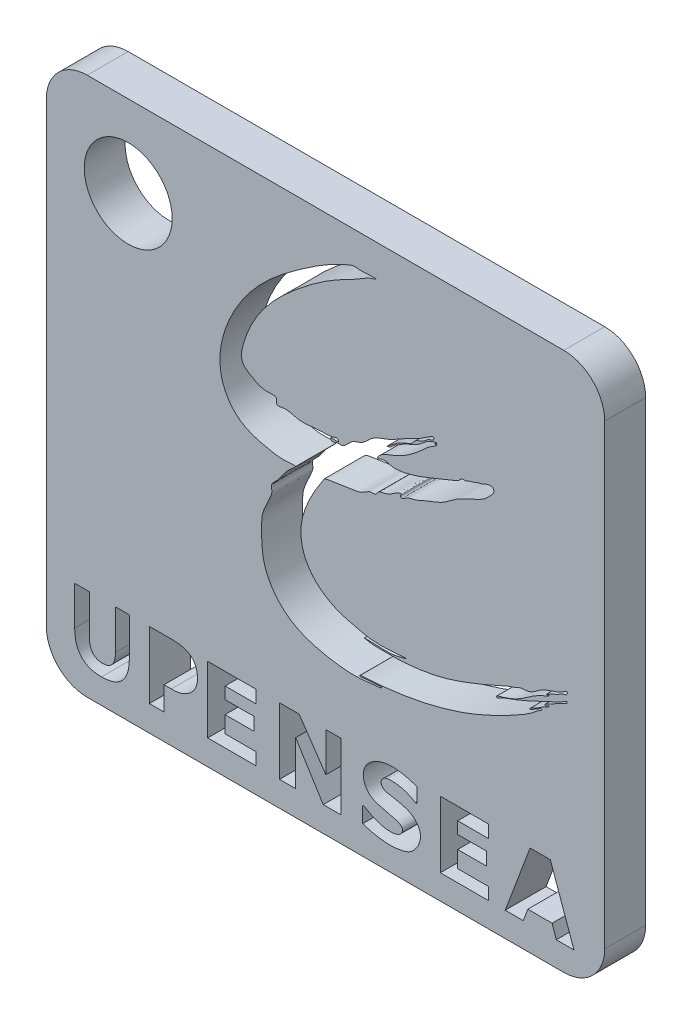
SolidWorks part; units mm, degrees
ref_plane "Plan de face" through (0, 0, 0) normal (0, 0, 1) x (1, 0, 0)
ref_plane "Plan de dessus" through (0, 0, 0) normal (0, 1, 0) x (1, 0, 0)
ref_plane "Plan de droite" through (0, 0, 0) normal (1, 0, 0) x (0, 0, -1)
sketch "Esquisse1" plane through (0, 0, 0) normal (0, 0, 1) x (1, 0, 0)
  line L0 (-81.1421, -32.8342) -> (-69.3736, -32.8342)
  line L1 (-69.3736, -32.8342) -> (-69.3736, -35.921)
  line L2 (-69.3736, -35.921) -> (-76.8977, -35.921)
  line L3 (-76.8977, -35.921) -> (-76.8977, -38.8149)
  line L4 (-76.8977, -38.8149) -> (-69.8674, -38.8149)
  line L5 (-69.8674, -38.8149) -> (-69.8674, -41.9917)
  line L6 (-69.8674, -41.9917) -> (-76.8977, -41.9917)
  line L7 (-76.8977, -41.9917) -> (-76.8977, -46.0504)
  line L8 (-76.8977, -46.0504) -> (-69.3736, -46.0504)
  line L9 (-69.3736, -46.0504) -> (-69.3736, -49.04)
  line L10 (-69.3736, -49.04) -> (-81.1421, -49.04)
  line L11 (-81.1421, -49.04) -> (-81.1421, -32.8342)
  line L12 (-63.6027, -32.8342) -> (-58.792, -32.8342)
  line L13 (-58.792, -32.8342) -> (-52.2677, -42.3901)
  line L14 (-52.2677, -42.3901) -> (-52.2677, -32.8342)
  line L15 (-52.2677, -32.8342) -> (-48.5742, -32.8342)
  line L16 (-48.5742, -32.8342) -> (-48.5742, -49.04)
  line L17 (-48.5742, -49.04) -> (-52.9133, -49.04)
  line L18 (-52.9133, -49.04) -> (-59.644, -38.2361)
  line L19 (-59.644, -38.2361) -> (-59.644, -49.04)
  line L20 (-59.644, -49.04) -> (-63.6027, -49.04)
  line L21 (-63.6027, -49.04) -> (-63.6027, -32.8342)
  line L22 (-24.3175, -32.95) -> (-12.549, -32.95)
  line L23 (-12.549, -32.95) -> (-12.549, -36.0368)
  line L24 (-12.549, -36.0368) -> (-20.0731, -36.0368)
  line L25 (-20.0731, -36.0368) -> (-20.0731, -38.9307)
  line L26 (-20.0731, -38.9307) -> (-13.0428, -38.9307)
  line L27 (-13.0428, -38.9307) -> (-13.0428, -42.1075)
  line L28 (-13.0428, -42.1075) -> (-20.0731, -42.1075)
  line L29 (-20.0731, -42.1075) -> (-20.0731, -46.1662)
  line L30 (-20.0731, -46.1662) -> (-12.549, -46.1662)
  line L31 (-12.549, -46.1662) -> (-12.549, -49.1558)
  line L32 (-12.549, -49.1558) -> (-24.3175, -49.1558)
  line L33 (-24.3175, -49.1558) -> (-24.3175, -32.95)
  line L34 (-2.3808, -32.95) -> (-8.462, -49.1558)
  line L35 (-4.0553, -49.1558) -> (-2.9335, -46.1662)
  line L36 (-2.9335, -46.1662) -> (3.0043, -46.1662)
  line L37 (3.0043, -46.1662) -> (4.0312, -49.1558)
  line L38 (4.0312, -49.1558) -> (8.3413, -49.1558)
  line L39 (8.3413, -49.1558) -> (2.5681, -32.95)
  line L40 (2.5681, -32.95) -> (-2.3808, -32.95)
  line L41 (0.0936, -37.3658) -> (1.9922, -42.8931)
  line L42 (1.9922, -42.8931) -> (-1.9654, -42.8931)
  line L43 (-1.9654, -42.8931) -> (0.0936, -37.3658)
  line L44 (-4.0553, -49.1558) -> (-8.462, -49.1558)
  line L45 (-30.0084, -33.7556) -> (-30.0084, -37.3658)
  line L46 (-30.0084, -37.3658) -> (-30.4403, -37.3658)
  line L47 (-43.2668, -44.5326) -> (-43.2668, -48.2453)
  line L49 (-120.5635, 76.467) -> (15.8561, 76.467)
  line L50 (-120.5635, 76.467) -> (-120.5635, -55.1571)
  line L51 (-120.5635, -55.1571) -> (15.8561, -55.1571)
  line L52 (15.8561, 76.467) -> (15.8561, -55.1571)
  circle A0 centre (-100.5635, 56.467) radius 10.7431
  spline S0 degree 3 poles (-52.6521, 20.0262) (-55.3334, 15.9515) (-60.2486, 7.9887) (-56.1162, -2.7779) (-49.9463, -6.2531) (-43.7235, -7.7216) (-40.6217, -8.8443) (-31.2107, -7.7102) (-35.4931, -8.7951) (-37.2317, -9.0197) (-44.5779, -8.4799) (-40.3233, -9.2515) (-38.1518, -9.1057) (-34.4042, -9.2177) (-29.4978, -8.7751) (-20.8331, -7.3091) (-9.8092, -2.3246) (-7.1565, -1.1405) (-5.6286, -0.6952) (-4.9048, -0.2341) (-3.9906, -0.1272) (-1.9518, -0.1849) (-0.2604, 1.9411) (3.4935, 3.0196) (5.3244, 3.8516) (6.7532, 4.8305) (6.7243, 3.7436) (5.7681, 3.7921) (4.2536, 2.7443) (3.1571, 2.4856) (1.5619, 1.5963) (1.9771, 1.4735) (2.3772, 1.8572) (2.2067, 1.5592) (2.1336, 1.4391) (2.1304, 1.4338) knots 0 0 0 0 0.034118 0.050236 0.068967 0.0735 0.095563 0.104191 0.107922 0.116908 0.126964 0.13031 0.137621 0.14482 0.154993 0.171422 0.207781 0.216896 0.21919 0.229442 0.232265 0.24613 0.386673 0.489154 0.601852 0.608768 0.628384 0.656974 0.686943 0.800375 0.806976 0.814482 0.827885 0.837106 0.837535 0.837535 0.837535 0.837535
  spline S1 degree 3 poles (2.1304, 1.4338) (-3.2143, -0.4983) (-3.5636, -3.1574) (-10.7433, -4.8196) (-10.4207, -5.2619) (-10.0076, -5.0191) (-9.1355, -4.4797) (-6.2924, -3.5462) (-2.2057, -1.8343) (2.6217, 0.5739) (5.1274, 1.6237) (6.7268, 2.6931) (6.7061, 2.0367) (6.1892, 2.0349) (5.6903, 1.5221) (4.621, 1.2435) (3.4802, 0.3835) (2.2151, -0.1297) (1.5935, -0.5477) (1.0869, -0.7912) (1.5087, -1.1167) (1.7441, -0.7689) (2.0279, -0.5527) (2.3778, -0.8038) (1.8965, -0.8769) (1.6097, -1.1864) (0.7544, -1.491) (-0.2683, -2.2868) (-1.4781, -2.9352) (-2.2533, -3.2224) (-2.5669, -3.6281) (-1.7593, -3.506) (-1.4045, -2.961) (-0.3761, -2.6651) (0.0243, -2.1587) (0.5176, -2.1417) (0.3842, -2.5623) (-0.1273, -2.6442) (-0.7211, -3.1586) (-2.3341, -4.566) (-7.4709, -7.5112) (-19.2478, -13.4595) (-32.514, -16.378) (-41.7877, -17.0094) (-43.6311, -17.0895) (-43.832, -17.1275) (-44.0811, -17.3149) (-43.5984, -17.4832) (-43.0648, -17.2603) (-42.2857, -17.3044) (-41.9929, -17.2707) knots 0 0 0 0 0.134848 0.143034 0.144602 0.148639 0.15418 0.178068 0.234678 0.292201 0.330746 0.333193 0.337239 0.34163 0.346585 0.358072 0.373748 0.389768 0.396913 0.399366 0.402749 0.405986 0.410304 0.412056 0.415103 0.419095 0.426513 0.440579 0.458948 0.465949 0.467501 0.470952 0.480464 0.491217 0.499184 0.500837 0.502285 0.509316 0.515196 0.525664 0.573905 0.691977 0.923329 0.972552 0.974531 0.977935 0.97947 0.981332 0.988582 1 1 1 1
  spline S2 degree 3 poles (-41.9929, -17.2707) (-41.9788, -17.2837) (-39.8428, -17.181) (-38.755, -16.9729) (-38.5663, -17.0696) (-38.6975, -17.3571) (-38.8106, -17.3428) (-38.9909, -17.3428) knots 0 0 0 0 0.789101 0.825842 0.866785 0.917494 1 1 1 1
  spline S3 degree 3 poles (-38.9909, -17.3428) (-41.4072, -17.6298) (-45.2552, -18.1586) (-52.8341, -17.1941) (-61.3994, -15.1557) (-68.0331, -6.4333) (-67.9639, 0.274) (-67.9478, 5.786) (-66.0715, 8.6338) (-65.3184, 11.1565) (-65.8748, 12.393) (-64.1051, 13.8198) (-62.6773, 15.9813) (-61.4735, 17.5888) (-59.1059, 19.3906) (-63.2666, 18.8642) (-66.4685, 19.585) (-72.9268, 21.0498) (-80.9751, 30.5359) (-74.113, 49.4377) (-60.0056, 60.7329) (-50.3924, 66.8729) (-45.5535, 68.7199) (-44.2361, 68.5409) (-42.7435, 68.5663) (-38.9093, 68.8413) (-41.9561, 67.9964) (-44.3031, 66.3257) (-50.0489, 63.6386) (-58.0968, 58.1526) (-67.1463, 50.1111) (-71.8026, 41.7282) (-73.4928, 34.6163) (-69.7732, 32.4272) (-67.6012, 31.1924) (-64.2264, 31.7212) (-64.3925, 30.572) (-64.2794, 29.6066) (-61.7144, 30.4334) (-58.8055, 28.8928) (-54.2716, 29.9061) (-51.3045, 29.5246) (-49.4313, 30.3609) (-48.9, 29.4447) (-50.1299, 29.5407) (-51.4905, 29.5283) (-50.5578, 28.6216) (-49.637, 29.3856) (-47.6915, 28.9538) (-46.3674, 31.58) (-43.2546, 31.9776) (-40.8927, 35.0774) (-36.4966, 36.0563) (-31.9864, 39.1871) (-29.4686, 39.8946) (-25.6893, 42.7432) (-25.9981, 41.2912) (-27.0909, 41.3145) (-27.9761, 40.3733) (-29.141, 39.7498) (-30.483, 39.3097) (-31.3078, 37.9953) (-33.1588, 37.4839) (-35.0845, 36.3905) (-36.0606, 35.4678) (-37.8011, 34.347) (-36.1873, 34.9009) (-35.6812, 35.6441) (-34.2101, 36.4274) (-32.8831, 37.4122) (-30.9675, 38.0047) (-28.5056, 39.4567) (-27.3907, 41.0171) (-25.0035, 41.395) (-25.3264, 41.0299) (-25.3331, 41.1161) (-25.6368, 40.9763) knots 0 0 0 0 0.026687 0.041759 0.083493 0.118973 0.15054 0.156598 0.176995 0.180173 0.185825 0.19148 0.201603 0.213818 0.218107 0.223796 0.242243 0.2661 0.288782 0.36971 0.440445 0.490023 0.491708 0.496504 0.503315 0.512758 0.517467 0.527117 0.549028 0.582505 0.635087 0.675369 0.692164 0.702026 0.71711 0.724427 0.726292 0.728748 0.733278 0.748051 0.765921 0.779575 0.782783 0.784337 0.788152 0.791967 0.793474 0.798863 0.80206 0.813838 0.823241 0.834393 0.853281 0.871386 0.888313 0.896676 0.897774 0.902185 0.905809 0.911659 0.916426 0.920643 0.927543 0.936656 0.942844 0.946607 0.949758 0.954208 0.957935 0.967061 0.972246 0.979627 0.996876 0.997506 0.998263 1 1 1 1
  spline S4 degree 3 poles (-25.6368, 40.9763) (-25.6733, 40.8054) (-25.4242, 40.938) (-25.0658, 40.9051) (-25.4396, 40.5844) (-25.8747, 40.3011) (-26.9416, 39.7153) (-28.3291, 38.4028) (-31.0963, 35.9972) (-34.7385, 33.4962) (-38.854, 32.4513) (-39.6122, 31.096) (-39.7178, 30.921) (-39.2618, 30.8129) (-38.928, 31.1404) (-38.1449, 31.2357) (-37.2797, 31.2884) (-36.2001, 30.8875) (-34.9991, 30.7965) (-32.3007, 31.1843) (-28.8775, 32.2666) (-24.6192, 34.0657) (-21.6074, 35.2324) (-19.6403, 36.1048) (-19.1108, 36.9743) (-18.1402, 36.731) (-17.3166, 37.2696) (-16.1544, 37.4755) (-15.2088, 37.9964) (-14.0495, 38.132) (-13.2111, 38.6955) (-12.3008, 38.8984) (-11.3558, 38.8479) (-11.0854, 37.8223) (-11.9956, 36.8135) (-13.395, 35.2514) (-16.5811, 33.7226) (-20.3331, 32.1581) (-23.7739, 29.1421) (-27.355, 28.1263) (-30.3376, 26.5095) (-32.2613, 26.4358) (-33.7875, 25.052) (-34.1352, 25.8254) (-33.5394, 26.4287) (-34.8709, 25.9786) (-35.5281, 25.5291) (-36.741, 24.6683) (-38.1132, 24.2688) (-39.5275, 24.0111) (-40.0047, 22.7863) (-41.1338, 23.0436) (-42.3071, 22.5053) (-43.7847, 21.3791) (-46.3622, 21.215) (-49.3402, 20.5183) (-51.5236, 20.4601) (-52.6521, 20.0262) knots 0 0 0 0 0.003835 0.005626 0.00865 0.013337 0.025485 0.043794 0.074034 0.138519 0.186487 0.188036 0.18927 0.191769 0.197818 0.204074 0.215307 0.224789 0.239449 0.252379 0.309643 0.350812 0.396295 0.411559 0.416285 0.42557 0.437284 0.446181 0.46202 0.470349 0.48205 0.492444 0.500051 0.507958 0.519114 0.539936 0.574207 0.626742 0.667092 0.713693 0.742758 0.767935 0.781266 0.784831 0.790075 0.797681 0.809789 0.823175 0.84057 0.856115 0.863527 0.876386 0.884884 0.903947 0.932867 0.962689 1 1 1 1
  spline S5 degree 3 poles (-66.3705, -0.6372) (-66.2426, -3.307) (-66.2081, -4.4798) (-65.0585, -6.4613) (-63.8673, -8.1484) (-63.6964, -8.3653) (-63.7281, -8.1137) (-63.7348, -8.1525) (-63.8418, -7.9649) (-63.8834, -7.8805) (-63.9419, -7.6812) knots 0 0 0 0 0.53075 0.866804 0.910185 0.922558 0.935229 0.965645 0.972122 1 1 1 1
  spline S6 degree 3 poles (-63.9419, -7.6812) (-64.7159, -5.3195) (-65.7948, -3.066) (-66.3705, -0.6372) knots 0 0 0 0 1 1 1 1
  spline S7 degree 3 poles (-62.5352, -10.5523) (-63.6787, -9.4519) (-63.2343, -10.5737) (-62.6831, -11.0949) (-61.8406, -11.8438) (-61.4717, -12.1252) (-61.047, -12.4765) (-61.089, -12.1979) (-61.2166, -12.0257) (-61.5343, -11.6826) (-62.0825, -11.0825) (-62.5352, -10.5523) (-63.6787, -9.4519) (-63.2343, -10.5737) knots -0.402191 -0.295019 -0.119537 0 0.066805 0.227094 0.37929 0.471781 0.501895 0.514205 0.563001 0.597809 0.704981 0.880463 1 1.066805 1.227094 1.37929 only from (-63.5047, -9.7729) to (-63.5047, -9.7729)
  spline S8 degree 3 poles (-30.0084, -33.7556) (-32.645, -32.8965) (-37.1136, -31.7547) (-42.1383, -34.3995) (-43.5351, -37.9134) (-42.2928, -41.3103) (-39.0211, -42.4726) (-36.4644, -43.0591) (-34.5429, -43.4994) (-33.4189, -44.3949) (-33.6635, -45.5813) (-34.9075, -46.4708) (-37.0204, -46.6611) (-39.6413, -46.0975) (-41.6577, -45.1439) (-42.7569, -44.4019) (-43.2336, -44.3001) (-43.2668, -44.5326) knots 0 0 0 0 0.213305 0.332543 0.387996 0.489669 0.562609 0.640595 0.690513 0.712561 0.740192 0.766735 0.824594 0.893931 0.970764 0.987194 1 1 1 1
  spline S9 degree 3 poles (-30.4403, -37.3658) (-32.1696, -36.2135) (-34.6764, -35.5022) (-37.9246, -35.6751) (-39.0034, -37.0045) (-38.3722, -38.5423) (-36.2028, -38.9167) (-33.6935, -39.3132) (-30.7247, -40.385) (-28.6088, -43.3373) (-29.6785, -46.5114) (-31.5752, -48.5521) (-36.1582, -49.9657) (-40.259, -49.2481) (-43.2668, -48.2453) knots 0 0 0 0 0.15292 0.204126 0.234845 0.267869 0.309745 0.39187 0.468931 0.544719 0.643629 0.695197 0.754799 1 1 1 1
  point P97 (-66.2687, -2.6021)
  point P315 (0, 0)
  dimension "D1" = 20
  dimension "D2" = 20
extrude "Boss.-Extru.1" add sketch "Esquisse1" along normal blind 10 contours L52 L49 L50 L51 S3 S4 S0 S1 S2 A0 L20 L21 L12 L13 L14 L15 L16 L17 L18 L19 L10 L11 L0 L1 L2 L3 L4 L5 L6 L7 L8 L9 L32 L33 L22 L23 L24 L25 L26 L27 L28 L29 L30 L31 L35
fillet "Congé1" radius 10 4 edges at (-120.5635, -55.1571, 5) (15.8561, -55.1571, 5) (-120.5635, 76.467, 5) (15.8561, 76.467, 5)
sketch "Esquisse2" plane through (0, 0, 10) normal (0, 0, 1) x (1, 0, 0)
  text T0 "<b>UP</b>" font "@Microsoft YaHei" height in points 57
extrude "Enlèv. mat.-Extru.1" cut sketch "Esquisse2" against normal blind 10
sketch "Esquisse3" plane through (0, 0, 10) normal (0, 0, 1) x (1, 0, 0)
  line L1 (-93.6316, -33.9447) -> (-86.5461, -33.9447)
  line L2 (-93.6316, -33.9447) -> (-93.6316, -41.6554)
  line L3 (-93.6316, -41.6554) -> (-86.5461, -41.6554)
  line L4 (-86.5461, -33.9447) -> (-86.5461, -41.6554)
extrude "Enlèv. mat.-Extru.2" cut sketch "Esquisse3" against normal blind 10
equation "\"éà\"=18"
